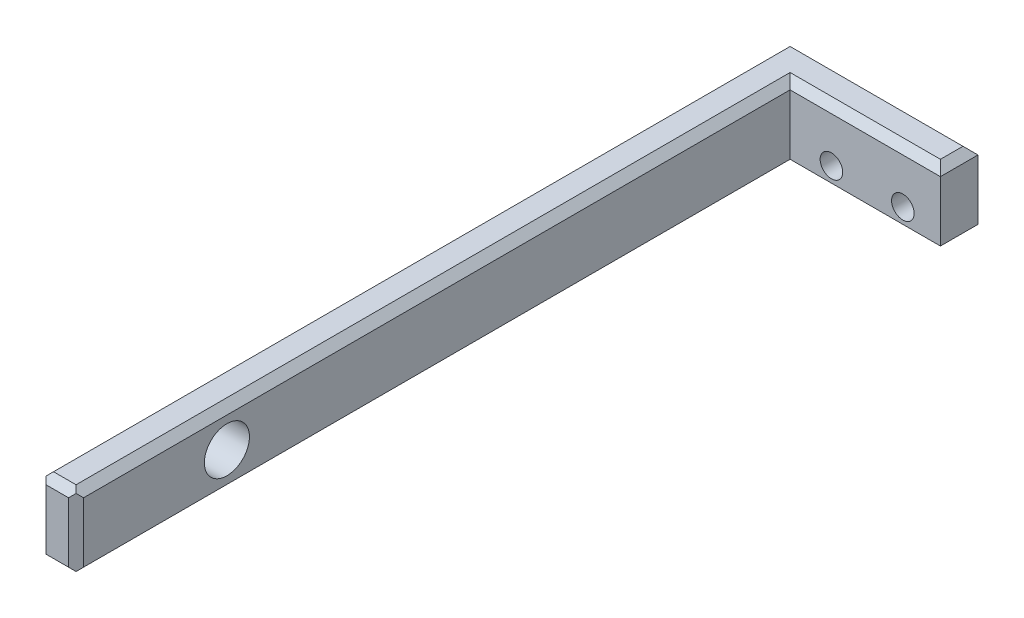
SolidWorks part; units mm, degrees
ref_plane "Front Plane" through (0, 0, 0) normal (0, 0, 1) x (1, 0, 0)
ref_plane "Top Plane" through (0, 0, 0) normal (0, 1, 0) x (1, 0, 0)
ref_plane "Right Plane" through (0, 0, 0) normal (1, 0, 0) x (0, 0, -1)
sketch "Sketch1" plane through (0, 0, 0) normal (0, 1, 0) x (1, 0, 0)
  line L0 (0, 0) -> (0, 100)
  line L1 (0, -55) -> (0, 55) construction
  line L2 (0, 100) -> (25, 100)
  line L3 (25, 100) -> (25, 95)
  line L4 (25, 95) -> (5, 95)
  line L5 (5, 95) -> (5, 0)
  line L6 (-55, 0) -> (55, 0) construction
  line L7 (5, 0) -> (0, 0)
  dimension "D1" = 25
  dimension "D2" = 5
  dimension "D3" = 5
  dimension "D4" = 100
extrude "Boss-Extrude1" add sketch "Sketch1" along normal blind 10
sketch "Sketch2" plane through (0, 0, 0) normal (1, 0, 0) x (0, 0, -1)
  line L0 (0, 5.5) -> (0, -5.5) construction
  line L1 (11, 0) -> (-11, 0) construction
  circle A0 centre (20.0695, 5) radius 3
  dimension "D1" = 6
  dimension "D2" = 20.0695
  dimension "D3" = 5
extrude "Cut-Extrude1" cut sketch "Sketch2" along normal blind 10
sketch "Sketch3" plane through (0, 0, -100) normal (0, 0, -1) x (-1, 0, 0)
  line L0 (13.75, 0) -> (-13.75, 0) construction
  line L1 (-25, 10) -> (-25, 0) construction
  circle A0 centre (-20, 3) radius 1.5
  circle A1 centre (-10.5, 3) radius 1.5
  dimension "D1" = 3
  dimension "D2" = 3
  dimension "D3" = 3
  dimension "D4" = 3
  dimension "D5" = 5
  dimension "D6" = 9.5
extrude "Cut-Extrude2" cut sketch "Sketch3" against normal blind 20
chamfer "Chamfer1" distance 1 angle 45 6 edges at (0, 10, -50) (12.5, 10, -100) (25, 10, -97.5) (15, 10, -95) (5, 10, -47.5) (2.5, 10, 0)
chamfer "Chamfer2" distance 1 angle 45 6 edges at (5, 0, -47.5) (15, 0, -95) (25, 0, -97.5) (12.5, 0, -100) (0, 0, -50) (2.5, 0, 0)
chamfer "Chamfer3" distance 1 angle 45 1 edges at (0, 5, -100)
chamfer "Chamfer4" distance 1 angle 45 2 edges at (0, 5, 0) (5, 5, 0)
